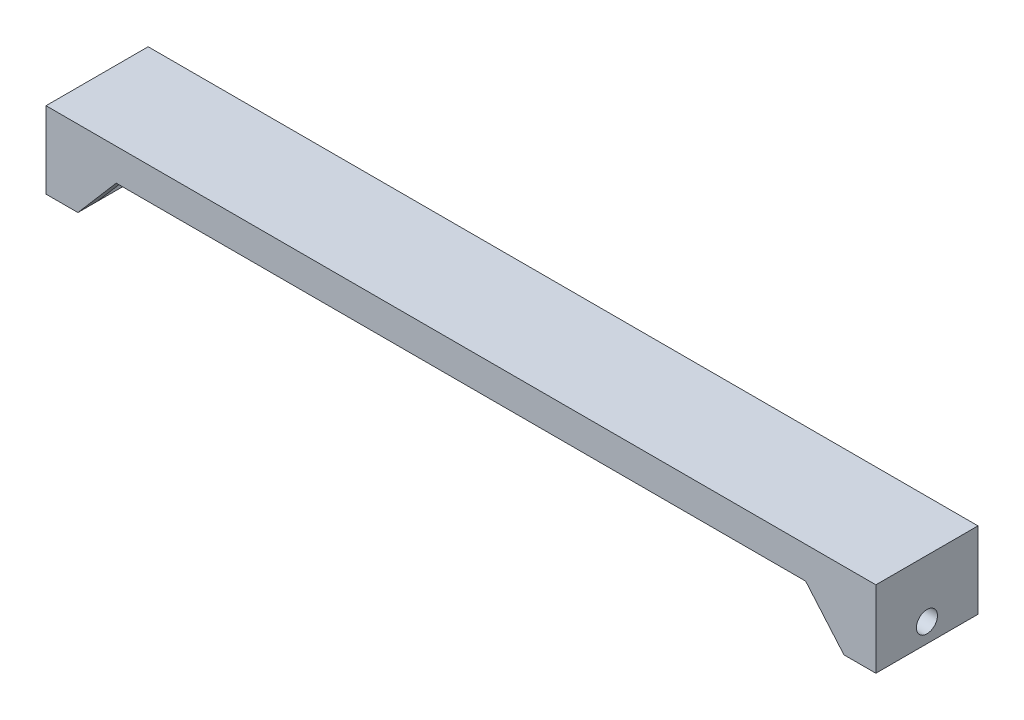
SolidWorks part; units mm, degrees
ref_plane "前视基准面" through (0, 0, 0) normal (0, 0, 1) x (1, 0, 0)
ref_plane "上视基准面" through (0, 0, 0) normal (0, 1, 0) x (1, 0, 0)
ref_plane "右视基准面" through (0, 0, 0) normal (1, 0, 0) x (0, 0, -1)
sketch "草图1" plane through (0, 0, 0) normal (0, 0, 1) x (1, 0, 0)
  line L0 (-65, 0) -> (65, 0)
  line L1 (65, 0) -> (65, -12)
  line L2 (65, -12) -> (60, -12)
  line L3 (60, -12) -> (60, -5)
  line L4 (60, -5) -> (-60, -5)
  line L5 (-60, -5) -> (-60, -12)
  line L6 (-60, -12) -> (-65, -12)
  line L7 (-65, -12) -> (-65, 0)
  line L8 (0, -7.4248) -> (0, 9.2484) construction
  dimension "D1" = 5
  dimension "D2" = 5
  dimension "D3" = 130
  dimension "D4" = 12
  dimension "D5" = 12
extrude "凸台-拉伸2" add sketch "草图1" along normal blind 16
sketch "草图3" plane through (-60, 0, 0) normal (1, 0, 0) x (0, 0, -1)
  line L0 (-16, 0) -> (-16, -12) construction
  line L1 (-16, -12) -> (0, -12) construction
  circle A0 centre (-8, -9) radius 1.65
  dimension "D2" = 3.3
  dimension "D1" = 3
  dimension "D3" = 8
extrude "切除-拉伸1" cut sketch "草图3" against normal through all both and the other way through all
sketch "草图4" plane through (0, 0, 0) normal (0, 0, -1) x (-1, 0, 0)
  line L0 (54, -5) -> (60, -12)
  line L1 (60, -5) -> (-60, -5) construction
  line L2 (54, -5) -> (60, -5)
  line L4 (60, -5) -> (60, -12)
  dimension "D1" = 6
extrude "凸台-拉伸3" add sketch "草图4" against normal blind 3
sketch "草图5" plane through (0, -5, 0) normal (0, -1, 0) x (1, 0, 0)
  line L0 (60, 8) -> (-60, 8) construction
  line L1 (60, 16) -> (60, 0) construction
  line L2 (-60, 16) -> (-60, 3) construction
ref_plane "基准面3" through (0, 0, 8) normal (0, 0, 1) x (1, 0, 0)
mirror "镜向1" about plane through (0, 0, 8) normal (0, 0, 1) of "凸台-拉伸3"
mirror "镜向2" about plane through (0, 0, 0) normal (1, 0, 0) of "镜向1", "凸台-拉伸3"
